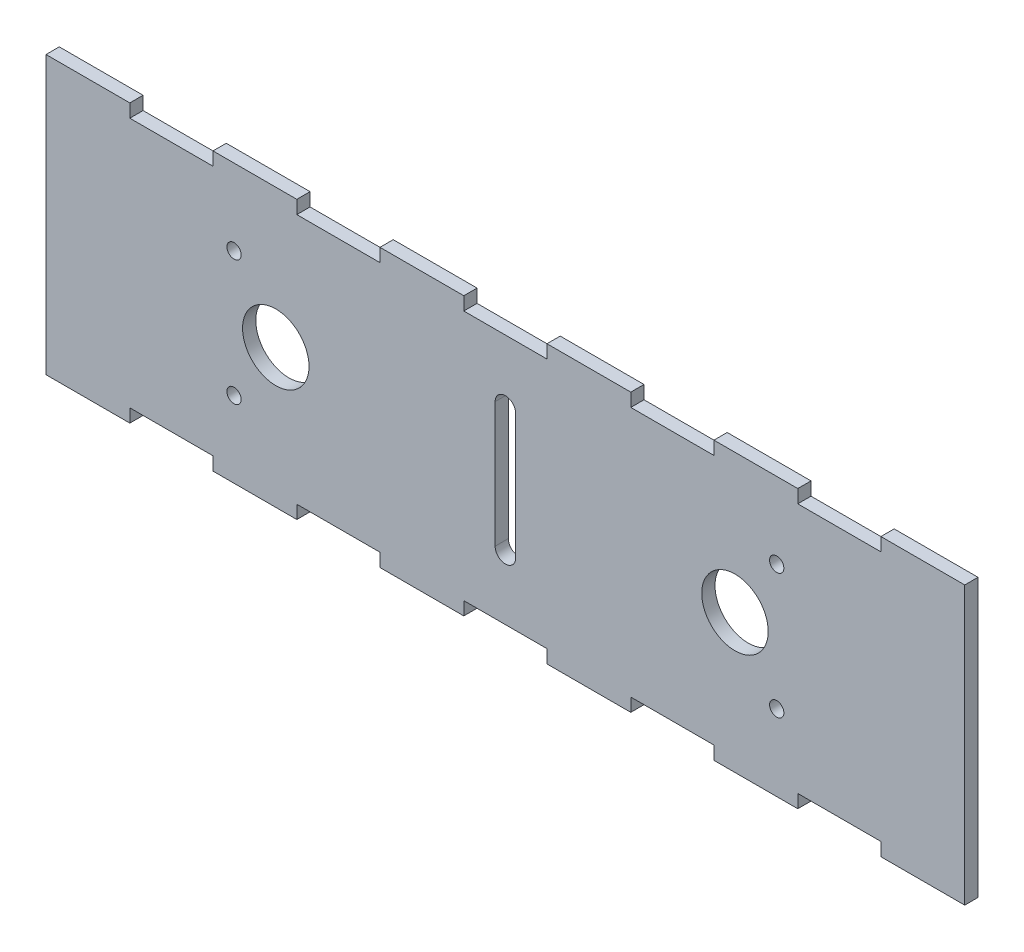
SolidWorks part; units mm, degrees
ref_plane "Front Plane" through (0, 0, 0) normal (0, 0, 1) x (1, 0, 0)
ref_plane "Top Plane" through (0, 0, 0) normal (0, 1, 0) x (1, 0, 0)
ref_plane "Right Plane" through (0, 0, 0) normal (1, 0, 0) x (0, 0, -1)
sketch "Sketch1" plane through (0, 0, 0) normal (0, 0, 1) x (1, 0, 0)
  line L0 (-70, 30) -> (-70, 33.175)
  line L1 (-110, 30) -> (110, 30)
  line L2 (-110, 30) -> (-110, -30)
  line L3 (-110, -30) -> (110, -30)
  line L4 (110, 30) -> (110, -30)
  line L5 (-110, 30) -> (-90, 30)
  line L6 (-110, 30) -> (-110, 33.175)
  line L7 (-110, 33.175) -> (-90, 33.175)
  line L8 (-90, 30) -> (-90, 33.175)
  line L9 (-70, 33.175) -> (-50, 33.175)
  line L10 (-50, 30) -> (-50, 33.175)
  line L11 (-30, 30) -> (-30, 33.175)
  line L12 (-30, 33.175) -> (-10, 33.175)
  line L13 (-10, 30) -> (-10, 33.175)
  line L14 (10, 30) -> (10, 33.175)
  line L15 (10, 33.175) -> (30, 33.175)
  line L16 (30, 30) -> (30, 33.175)
  line L17 (50, 30) -> (50, 33.175)
  line L18 (50, 33.175) -> (70, 33.175)
  line L19 (70, 30) -> (70, 33.175)
  line L20 (90, 30) -> (90, 33.175)
  line L21 (90, 33.175) -> (110, 33.175)
  line L22 (110, 30) -> (110, 33.175)
  line L23 (-110, 0) -> (110, 0) construction
  line L24 (110, -30) -> (110, -33.175)
  line L25 (90, -33.175) -> (110, -33.175)
  line L26 (90, -30) -> (90, -33.175)
  line L27 (70, -30) -> (70, -33.175)
  line L28 (50, -33.175) -> (70, -33.175)
  line L29 (50, -30) -> (50, -33.175)
  line L30 (30, -30) -> (30, -33.175)
  line L31 (10, -30) -> (10, -33.175)
  line L32 (10, -33.175) -> (30, -33.175)
  line L33 (-10, -30) -> (-10, -33.175)
  line L34 (-30, -33.175) -> (-10, -33.175)
  line L35 (-30, -30) -> (-30, -33.175)
  line L36 (-50, -30) -> (-50, -33.175)
  line L37 (-70, -30) -> (-70, -33.175)
  line L38 (-70, -33.175) -> (-50, -33.175)
  line L39 (-90, -30) -> (-90, -33.175)
  line L40 (-110, -30) -> (-110, -33.175)
  line L41 (-110, -33.175) -> (-90, -33.175)
  line L42 (0, 30) -> (0, -30) construction
  line L43 (-65, 15) -> (-65, -15) construction
  line L44 (2.5, -15) -> (-2.5, -15)
  line L45 (2.5, -15) -> (2.5, 15)
  line L46 (2.5, 15) -> (-2.5, 15)
  line L47 (-2.5, -15) -> (-2.5, 15)
  line L48 (2.5, -15) -> (-2.5, 15) construction
  line L49 (2.5, 15) -> (-2.5, -15) construction
  line L50 (65, 15) -> (65, -15) construction
  arc A70 (2.5, 15) -> (-2.5, 15) centre (0, 15) ccw
  arc A71 (2.5, -15) -> (-2.5, -15) centre (0, -15) cw
  circle A72 centre (-65, 15) radius 1.755
  circle A73 centre (-65, -15) radius 1.755
  circle A74 centre (65, -15) radius 1.755
  circle A75 centre (65, 15) radius 1.755
  circle A103 centre (0, 0) radius 2.5
  circle A104 centre (55, 0) radius 8
  circle A105 centre (-55, 0) radius 8
  point P72 (-65, 0)
  point P79 (65, 0)
  dimension "D8" = 5
  dimension "D9" = 16
  dimension "D10" = 16
  dimension "D16" = 3.51
  dimension "D1" = 220
  dimension "D2" = 60
  dimension "D3" = 110
  dimension "D4" = 30
  dimension "D5" = 3.175
  dimension "D6" = 20
  dimension "D11" = 30
  dimension "D12" = 55
  dimension "D13" = 55
  dimension "D14" = 30
  dimension "D15" = 5
  dimension "D17" = 30
  dimension "D18" = 10
  dimension "D7" = 6
extrude "Boss-Extrude1" add sketch "Sketch1" along normal blind 3.175
sketch "Sketch2" plane through (0, 0, 3.175) normal (0, 0, 1) x (1, 0, 0)
  line L53 (2.4594, -15) -> (2.4594, 15)
  line L54 (-2.4594, 15) -> (-2.4594, -15)
  line L55 (2.4594, -15) -> (2.4594, 15)
  line L56 (-2.4594, 15) -> (-2.4594, -15)
  line L88 (110.0406, -33.2156) -> (110.0406, 33.2156)
  line L89 (110.0406, 33.2156) -> (89.9594, 33.2156)
  line L90 (89.9594, 33.2156) -> (89.9594, 30.0406)
  line L91 (89.9594, 30.0406) -> (70.0406, 30.0406)
  line L92 (70.0406, 30.0406) -> (70.0406, 33.2156)
  line L93 (70.0406, 33.2156) -> (49.9594, 33.2156)
  line L94 (49.9594, 33.2156) -> (49.9594, 30.0406)
  line L95 (49.9594, 30.0406) -> (30.0406, 30.0406)
  line L96 (30.0406, 30.0406) -> (30.0406, 33.2156)
  line L97 (30.0406, 33.2156) -> (9.9594, 33.2156)
  line L98 (9.9594, 33.2156) -> (9.9594, 30.0406)
  line L99 (9.9594, 30.0406) -> (-9.9594, 30.0406)
  line L100 (-9.9594, 30.0406) -> (-9.9594, 33.2156)
  line L101 (-9.9594, 33.2156) -> (-30.0406, 33.2156)
  line L102 (-30.0406, 33.2156) -> (-30.0406, 30.0406)
  line L103 (-30.0406, 30.0406) -> (-49.9594, 30.0406)
  line L104 (-49.9594, 30.0406) -> (-49.9594, 33.2156)
  line L105 (-49.9594, 33.2156) -> (-70.0406, 33.2156)
  line L106 (-70.0406, 33.2156) -> (-70.0406, 30.0406)
  line L107 (-70.0406, 30.0406) -> (-89.9594, 30.0406)
  line L108 (-89.9594, 30.0406) -> (-89.9594, 33.2156)
  line L109 (-89.9594, 33.2156) -> (-110.0406, 33.2156)
  line L110 (-110.0406, 33.2156) -> (-110.0406, -33.2156)
  line L111 (-110.0406, -33.2156) -> (-89.9594, -33.2156)
  line L112 (-89.9594, -33.2156) -> (-89.9594, -30.0406)
  line L113 (-89.9594, -30.0406) -> (-70.0406, -30.0406)
  line L114 (-70.0406, -30.0406) -> (-70.0406, -33.2156)
  line L115 (-70.0406, -33.2156) -> (-49.9594, -33.2156)
  line L116 (-49.9594, -33.2156) -> (-49.9594, -30.0406)
  line L117 (-49.9594, -30.0406) -> (-30.0406, -30.0406)
  line L118 (-30.0406, -30.0406) -> (-30.0406, -33.2156)
  line L119 (-30.0406, -33.2156) -> (-9.9594, -33.2156)
  line L120 (-9.9594, -33.2156) -> (-9.9594, -30.0406)
  line L121 (-9.9594, -30.0406) -> (9.9594, -30.0406)
  line L122 (9.9594, -30.0406) -> (9.9594, -33.2156)
  line L123 (9.9594, -33.2156) -> (30.0406, -33.2156)
  line L124 (30.0406, -33.2156) -> (30.0406, -30.0406)
  line L125 (30.0406, -30.0406) -> (49.9594, -30.0406)
  line L126 (49.9594, -30.0406) -> (49.9594, -33.2156)
  line L127 (49.9594, -33.2156) -> (70.0406, -33.2156)
  line L128 (70.0406, -33.2156) -> (70.0406, -30.0406)
  line L129 (70.0406, -30.0406) -> (89.9594, -30.0406)
  line L130 (89.9594, -30.0406) -> (89.9594, -33.2156)
  line L131 (89.9594, -33.2156) -> (110.0406, -33.2156)
  line L132 (110.0406, -33.2156) -> (110.0406, 33.2156)
  line L133 (110.0406, 33.2156) -> (89.9594, 33.2156)
  line L134 (89.9594, 33.2156) -> (89.9594, 30.0406)
  line L135 (89.9594, 30.0406) -> (70.0406, 30.0406)
  line L136 (70.0406, 30.0406) -> (70.0406, 33.2156)
  line L137 (70.0406, 33.2156) -> (49.9594, 33.2156)
  line L138 (49.9594, 33.2156) -> (49.9594, 30.0406)
  line L139 (49.9594, 30.0406) -> (30.0406, 30.0406)
  line L140 (30.0406, 30.0406) -> (30.0406, 33.2156)
  line L141 (30.0406, 33.2156) -> (9.9594, 33.2156)
  line L142 (9.9594, 33.2156) -> (9.9594, 30.0406)
  line L143 (9.9594, 30.0406) -> (-9.9594, 30.0406)
  line L144 (-9.9594, 30.0406) -> (-9.9594, 33.2156)
  line L145 (-9.9594, 33.2156) -> (-30.0406, 33.2156)
  line L146 (-30.0406, 33.2156) -> (-30.0406, 30.0406)
  line L147 (-30.0406, 30.0406) -> (-49.9594, 30.0406)
  line L148 (-49.9594, 30.0406) -> (-49.9594, 33.2156)
  line L149 (-49.9594, 33.2156) -> (-70.0406, 33.2156)
  line L150 (-70.0406, 33.2156) -> (-70.0406, 30.0406)
  line L151 (-70.0406, 30.0406) -> (-89.9594, 30.0406)
  line L152 (-89.9594, 30.0406) -> (-89.9594, 33.2156)
  line L153 (-89.9594, 33.2156) -> (-110.0406, 33.2156)
  line L154 (-110.0406, 33.2156) -> (-110.0406, -33.2156)
  line L155 (-110.0406, -33.2156) -> (-89.9594, -33.2156)
  line L156 (-89.9594, -33.2156) -> (-89.9594, -30.0406)
  line L157 (-89.9594, -30.0406) -> (-70.0406, -30.0406)
  line L158 (-70.0406, -30.0406) -> (-70.0406, -33.2156)
  line L159 (-70.0406, -33.2156) -> (-49.9594, -33.2156)
  line L160 (-49.9594, -33.2156) -> (-49.9594, -30.0406)
  line L161 (-49.9594, -30.0406) -> (-30.0406, -30.0406)
  line L162 (-30.0406, -30.0406) -> (-30.0406, -33.2156)
  line L163 (-30.0406, -33.2156) -> (-9.9594, -33.2156)
  line L164 (-9.9594, -33.2156) -> (-9.9594, -30.0406)
  line L165 (-9.9594, -30.0406) -> (9.9594, -30.0406)
  line L166 (9.9594, -30.0406) -> (9.9594, -33.2156)
  line L167 (9.9594, -33.2156) -> (30.0406, -33.2156)
  line L168 (30.0406, -33.2156) -> (30.0406, -30.0406)
  line L169 (30.0406, -30.0406) -> (49.9594, -30.0406)
  line L170 (49.9594, -30.0406) -> (49.9594, -33.2156)
  line L171 (49.9594, -33.2156) -> (70.0406, -33.2156)
  line L172 (70.0406, -33.2156) -> (70.0406, -30.0406)
  line L173 (70.0406, -30.0406) -> (89.9594, -30.0406)
  line L174 (89.9594, -30.0406) -> (89.9594, -33.2156)
  line L175 (89.9594, -33.2156) -> (110.0406, -33.2156)
  circle A2 centre (-55, 0) radius 7.9594
  circle A3 centre (-55, 0) radius 7.9594
  circle A5 centre (-65, 15) radius 1.7144
  circle A6 centre (-65, 15) radius 1.7144
  circle A8 centre (-65, -15) radius 1.7144
  circle A9 centre (-65, -15) radius 1.7144
  arc A14 (-2.4594, -15) -> (2.4594, -15) centre (0, -15) ccw
  arc A15 (2.4594, 15) -> (-2.4594, 15) centre (0, 15) ccw
  arc A16 (-2.4594, -15) -> (2.4594, -15) centre (0, -15) ccw
  arc A17 (2.4594, 15) -> (-2.4594, 15) centre (0, 15) ccw
  circle A18 centre (55, 0) radius 7.9594
  circle A19 centre (55, 0) radius 7.9594
  circle A21 centre (65, 15) radius 1.7144
  circle A22 centre (65, 15) radius 1.7144
  circle A24 centre (65, -15) radius 1.7144
  circle A25 centre (65, -15) radius 1.7144
  dimension "D1" = 0.0406
  dimension "D2" = 0.0406
  dimension "D3" = 0.0406
  dimension "D4" = 0.0406
  dimension "D5" = 0.0406
  dimension "D6" = 0.0406
  dimension "D7" = 0.0406
  dimension "D8" = 0.0406
extrude "Boss-Extrude2" add sketch "Sketch2" against normal blind 3.175
equation "\"stepper width\"=4.23"
equation "\"stepper hole disctance\"= 3.1"
equation "\"stepper hole diameter\"= 0.5"
equation "\"stepper shaft hole\"=2.4"
equation "\"tooth width\"=0.4"
equation "\"tooth thickness\"=0.3175"
equation "\"tooth to side\"=0.75"
equation "\"motor chamber height\"= 6"
equation "\"enclosure length\"= 22"
equation "\"platform diameter\"= 9cm"
equation "\"teeth width\"=0.3175"
equation "\"teeth lenght\"=2"
equation "\"tower width\"=7.7"
equation "\"D1@Sketch1\"=\"enclosure length\""
equation "\"D2@Sketch1\"=\"motor chamber height\""
equation "\"D3@Sketch1\"=\"enclosure length\"/2"
equation "\"D4@Sketch1\"=\"motor chamber height\"/2"
equation "\"D5@Sketch1\"=\"tooth thickness\""
equation "\"D6@Sketch1\"=\"teeth lenght\""
equation "\"D1@Boss-Extrude1\"=\"tooth thickness\""
equation "\"bearing outer diameter\"= 1.6"
equation "\"D8@Sketch1\"=\"stepper hole diameter\""
equation "\"D9@Sketch1\"=\"bearing outer diameter\""
equation "\"D10@Sketch1\"=\"bearing outer diameter\""
equation "\"half belt length\"=5.5"
equation "\"D12@Sketch1\"=\"half belt length\""
equation "\"D13@Sketch1\"=\"half belt length\""
equation "\"D14@Sketch1\"=\"platform diameter\"/3"
equation "\"D15@Sketch1\"=\"stepper hole diameter\""
equation "\"screw hole diameter\"=0.351"
equation "\"D16@Sketch1\"=\"screw hole diameter\""
equation "\"distance between screw hles\"=3"
equation "\"D17@Sketch1\"=\"distance between screw hles\""
